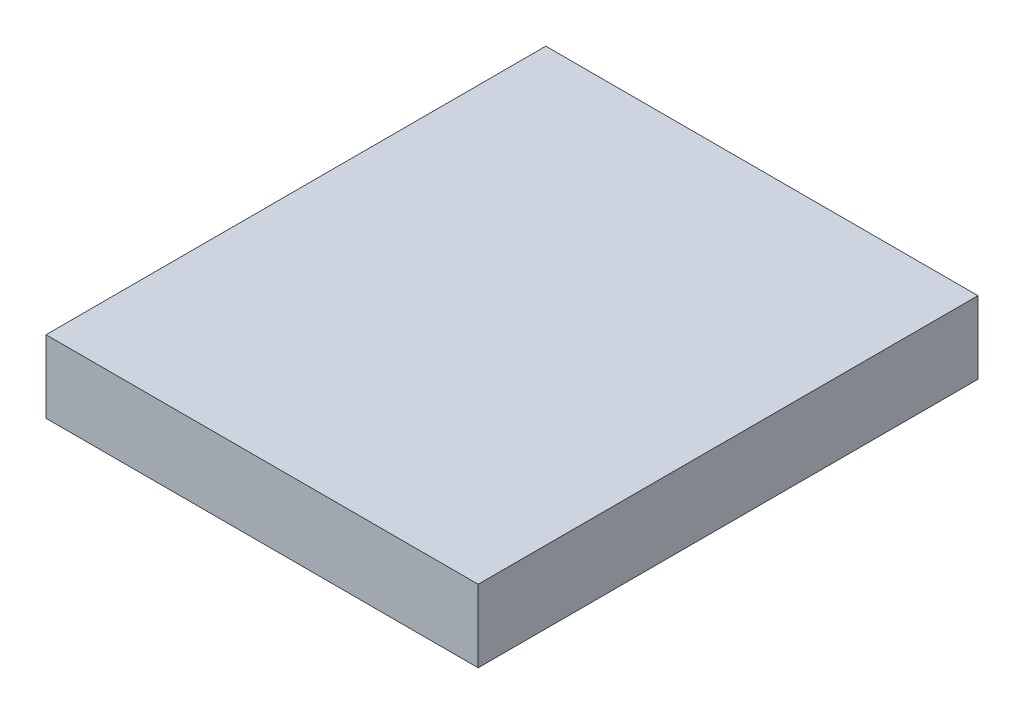
SolidWorks part; units mm, degrees
ref_plane "Front Plane" through (0, 0, 0) normal (0, 0, 1) x (1, 0, 0)
ref_plane "Top Plane" through (0, 0, 0) normal (0, 1, 0) x (1, 0, 0)
ref_plane "Right Plane" through (0, 0, 0) normal (1, 0, 0) x (0, 0, -1)
sketch "Sketch1" plane through (0, 0, 0) normal (0, 1, 0) x (1, 0, 0)
  line L1 (0, 0) -> (34.75, 0)
  line L2 (0, 0) -> (0, 40.19)
  line L3 (0, 40.19) -> (34.75, 40.19)
  line L4 (34.75, 0) -> (34.75, 40.19)
  dimension "D1" = 40.19
  dimension "D2" = 34.75
extrude "Boss-Extrude1" add sketch "Sketch1" along normal blind 5.82
equation "\"0.0529n\"=0.052"
